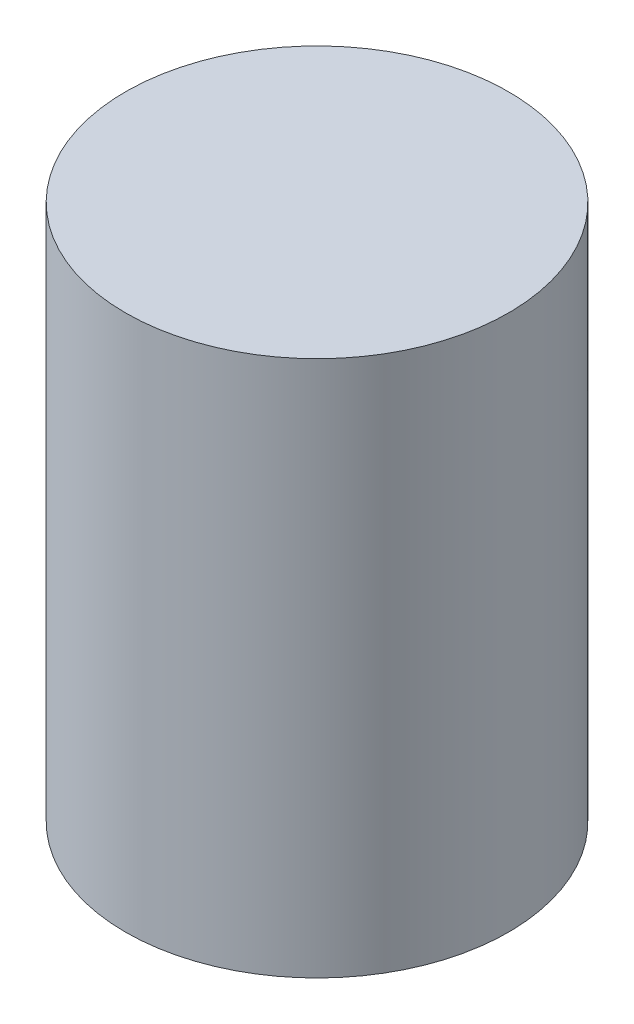
SolidWorks part; units mm, degrees
material "Polyethylene Cross-Linked"
ref_plane "Front Plane" through (0, 0, 0) normal (0, 0, 1) x (1, 0, 0)
ref_plane "Top Plane" through (0, 0, 0) normal (0, 1, 0) x (1, 0, 0)
ref_plane "Right Plane" through (0, 0, 0) normal (1, 0, 0) x (0, 0, -1)
sketch "Sketch1" plane through (0, 0, 0) normal (1, 0, 0) x (0, 0, -1)
  line L0 (0, 582.8344) -> (0, -483.9656) construction
  line L1 (0, 582.8344) -> (381, 582.8344)
  line L2 (381, 582.8344) -> (381, -483.9656)
  line L3 (381, -483.9656) -> (0, -483.9656)
  line L4 (0, 576.4844) -> (374.65, 576.4844)
  line L5 (374.65, 576.4844) -> (374.65, -477.6156)
  line L6 (374.65, -477.6156) -> (0, -477.6156)
  line L7 (0, -477.6156) -> (0, -483.9656)
  line L8 (0, 582.8344) -> (0, 576.4844)
  dimension "D1" = 1066.8
  dimension "D3" = 1066.8
  dimension "D4" = 381
  dimension "D2" = 6.35
revolve "Revolve1" add sketch "Sketch1" angle 360 about L8
